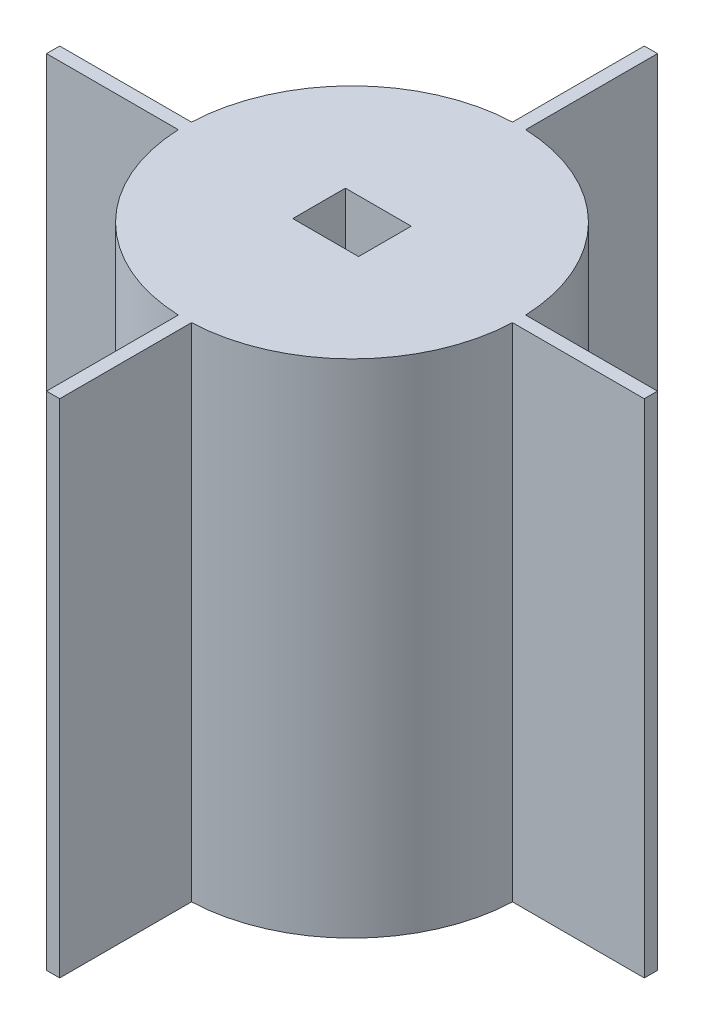
SolidWorks part; units mm, degrees
ref_plane "Front Plane" through (0, 0, 0) normal (0, 0, 1) x (1, 0, 0)
ref_plane "Top Plane" through (0, 0, 0) normal (0, 1, 0) x (1, 0, 0)
ref_plane "Right Plane" through (0, 0, 0) normal (1, 0, 0) x (0, 0, -1)
sketch "Sketch1" plane through (0, 0, 0) normal (0, 1, 0) x (1, 0, 0)
  circle A0 centre (0, 0) radius 12.7
  dimension "D1" = 25.4
extrude "Boss-Extrude1" add sketch "Sketch1" along normal blind 38.1
sketch "Sketch2" plane through (0, 38.1, 0) normal (0, 1, 0) x (1, 0, 0)
  line L1 (2.5, -2) -> (-2.5, -2)
  line L2 (2.5, -2) -> (2.5, 2)
  line L3 (2.5, 2) -> (-2.5, 2)
  line L4 (-2.5, -2) -> (-2.5, 2)
  line L5 (2.5, -2) -> (-2.5, 2) construction
  line L6 (2.5, 2) -> (-2.5, -2) construction
  point P0 (0, 0)
  dimension "D1" = 4
  dimension "D2" = 5
extrude "Cut-Extrude2" cut sketch "Sketch2" against normal blind 8
sketch "Sketch3" plane through (0, 0, 0) normal (0, -1, 0) x (1, 0, 0)
  line L0 (-22.7, 0.5) -> (-22.7, -0.5)
  line L1 (0, 0) -> (0, 18.521) construction
  line L2 (-12.7, 0.5) -> (-22.7, 0.5)
  line L3 (-12.7, -0.5) -> (-22.7, -0.5)
  line L4 (12.7, -0.5) -> (22.7, -0.5)
  line L5 (12.7, 0.5) -> (22.7, 0.5)
  line L6 (22.7, 0.5) -> (22.7, -0.5)
  line L8 (-22.7, 0.5) -> (-12.7, 0.5)
  line L9 (-22.7, 0.5) -> (-22.7, -0.5)
  line L10 (-22.7, -0.5) -> (-12.7, -0.5)
  circle A0 centre (0, 0) radius 12.7098
  point P1 (-12.6902, 0.5)
  point P2 (-12.6902, -0.5)
  point P14 (12.6902, -0.5)
  point P15 (12.6902, 0.5)
sketch "Sketch4" plane through (0, 38.1, 0) normal (0, 1, 0) x (1, 0, 0)
  line L0 (-12.6902, 0.5) -> (-22.7, 0.5)
  line L3 (-22.7, 0.5) -> (-22.7, -0.5)
  line L5 (22.7, 0.5) -> (22.7, -0.5)
  line L10 (-2.5, -0.5) -> (-22.7, -0.5)
  line L11 (-2.5, -0.5) -> (-2.5, 0.5)
  line L12 (-2.5, 0.5) -> (-22.7, 0.5)
  line L13 (-22.7, -0.5) -> (-22.7, 0.5)
  line L14 (2.5, 0.5) -> (22.7, 0.5)
  line L15 (2.5, 0.5) -> (2.5, -0.5)
  line L16 (2.5, -0.5) -> (22.7, -0.5)
  line L17 (22.7, 0.5) -> (22.7, -0.5)
  point P3 (-22.7, 0.5)
  point P8 (0, 0)
  point P9 (-22.7, -0.5)
  point P11 (22.7, 0.5)
  point P13 (22.7, -0.5)
  point P18 (-12.6902, 0.5)
  point P19 (-12.6902, 0.5)
  point P20 (-2.5, -0.5)
  point P22 (2.5, 0.5)
  dimension "D1" = 10.0098
sketch "Sketch5" plane through (0, 38.1, 0) normal (0, 1, 0) x (1, 0, 0)
  line L0 (-0.5, 22.7) -> (-0.5, 2.5)
  line L1 (-22.7, -0.5) -> (-2.5, -0.5)
  line L2 (-22.7, -0.5) -> (-22.7, 0.5)
  line L3 (-22.7, 0.5) -> (-2.5, 0.5)
  line L4 (-2.5, -0.5) -> (-2.5, 0.5)
  line L5 (2.5, -0.5) -> (22.7, -0.5)
  line L6 (2.5, -0.5) -> (2.5, 0.5)
  line L7 (2.5, 0.5) -> (22.7, 0.5)
  line L8 (22.7, -0.5) -> (22.7, 0.5)
  line L9 (-0.5, 22.7) -> (0.5, 22.7)
  line L10 (0.5, 22.7) -> (0.5, 2.5)
  line L11 (-0.5, 2.5) -> (0.5, 2.5)
  line L12 (22.7, 0.5) -> (2.5, 0.5)
  line L13 (22.7, 0.5) -> (22.7, -0.5)
  line L14 (22.7, -0.5) -> (2.5, -0.5)
  line L15 (2.5, 0.5) -> (2.5, -0.5)
  line L16 (0.5, -22.7) -> (0.5, -2.5)
  line L17 (0.5, -22.7) -> (-0.5, -22.7)
  line L18 (-0.5, -22.7) -> (-0.5, -2.5)
  line L19 (0.5, -2.5) -> (-0.5, -2.5)
  point P27 (0, 0)
  dimension "D1" = 4
extrude "Boss-Extrude2" add sketch "Sketch5" against normal up to surface (38.1 mm away) contours L7 L8 L5 L6 | L0 L11 L10 L9 | L3 L4 L1 L2 | L18 L19 L16 L17 up to face at (0, 0, 12.7)
sketch "Sketch6" plane through (0, 38.1, 0) normal (0, 1, 0) x (1, 0, 0)
  line L1 (2.5, -2) -> (-2.5, -2)
  line L2 (2.5, -2) -> (2.5, 2)
  line L3 (2.5, 2) -> (-2.5, 2)
  line L4 (-2.5, -2) -> (-2.5, 2)
  line L5 (2.5, -2) -> (-2.5, 2) construction
  line L6 (2.5, 2) -> (-2.5, -2) construction
  circle A0 centre (0, 0) radius 22.7055
extrude "Boss-Extrude3" [suppressed] add sketch "Sketch6" along normal blind 2.54 contours A0 | L2 L1 L4 L3
